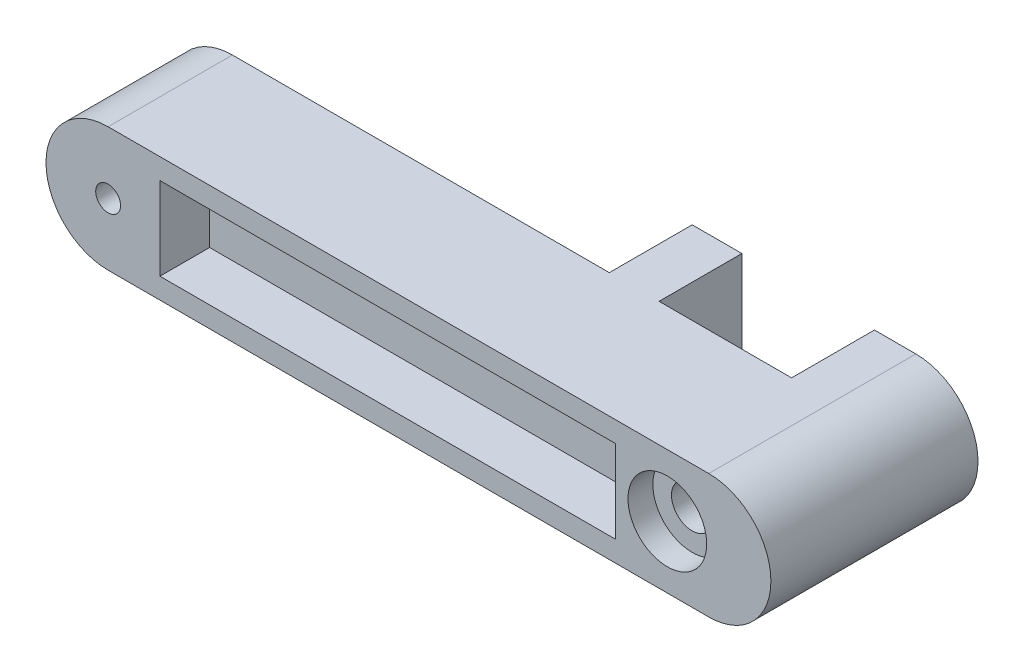
SolidWorks part; units mm, degrees
material "Custom Plastic"
ref_plane "Front Plane" through (0, 0, 0) normal (0, 0, 1) x (1, 0, 0)
ref_plane "Top Plane" through (0, 0, 0) normal (0, 1, 0) x (1, 0, 0)
ref_plane "Right Plane" through (0, 0, 0) normal (1, 0, 0) x (0, 0, -1)
other "Center of Mass"
sketch "Sketch1" plane through (0, 0, 0) normal (1, 0, 0) x (0, 0, -1)
  line L0 (0, 30) -> (135, 30)
  line L1 (135, 0) -> (0, 0)
  arc A0 (135, 30) -> (135, 0) centre (135, 15) cw
  arc A1 (0, 0) -> (0, 30) centre (0, 15) cw
  dimension "D1" = 135
  dimension "D2" = 30
extrude "Boss-Extrude1" add sketch "Sketch1" along normal blind 30
sketch "Sketch2" plane through (30, 0, 0) normal (1, 0, 0) x (0, 0, -1)
  circle A0 centre (0, 15) radius 3
  dimension "D1" = 6
extrude "Cut-Extrude1" cut sketch "Sketch2" against normal blind 30
sketch "Sketch3" plane through (30, 0, 0) normal (1, 0, 0) x (0, 0, -1)
  circle A0 centre (135, 15) radius 9.5
  dimension "D1" = 19
extrude "Cut-Extrude2" cut sketch "Sketch3" against normal blind 6
sketch "Sketch4" plane through (0, 0, 0) normal (-1, 0, 0) x (0, 0, 1)
  circle A0 centre (-135, 15) radius 9.5
  dimension "D1" = 19
extrude "Cut-Extrude3" cut sketch "Sketch4" against normal blind 6
sketch "Sketch5" plane through (6, 0, 0) normal (-1, 0, 0) x (0, 0, 1)
  circle A0 centre (-135, 15) radius 5
  dimension "D1" = 10
extrude "Cut-Extrude4" cut sketch "Sketch5" against normal up to next
scale "Scale1" [suppressed]
sketch "Sketch6" plane through (30, 0, 0) normal (1, 0, 0) x (0, 0, -1)
  line L1 (12.5, 25) -> (122.5, 25)
  line L2 (12.5, 25) -> (12.5, 5)
  line L3 (12.5, 5) -> (122.5, 5)
  line L4 (122.5, 25) -> (122.5, 5)
  line L5 (12.5, 25) -> (122.5, 5) construction
  line L6 (12.5, 5) -> (122.5, 25) construction
  point P0 (67.5, 15)
  dimension "D1" = 20
  dimension "D2" = 110
extrude "Cut-Extrude5" cut sketch "Sketch6" against normal blind 12
sketch "Sketch7" plane through (0, 0, 0) normal (-1, 0, 0) x (0, 0, 1)
  line L1 (-12.5, 5) -> (-122.5, 5)
  line L2 (-12.5, 5) -> (-12.5, 25)
  line L3 (-12.5, 25) -> (-122.5, 25)
  line L4 (-122.5, 5) -> (-122.5, 25)
  line L5 (-12.5, 5) -> (-122.5, 25) construction
  line L6 (-12.5, 25) -> (-122.5, 5) construction
  point P0 (-67.5, 15)
  dimension "D1" = 20
  dimension "D2" = 110
extrude "Cut-Extrude6" cut sketch "Sketch7" against normal blind 12
sketch "Sketch8" plane through (12, 0, 0) normal (-1, 0, 0) x (0, 0, 1)
  line L0 (-135, 30) -> (0, 30) construction
  line L1 (-103, 30) -> (-91, 30)
  line L2 (-103, 30) -> (-103, 0)
  line L3 (-103, 0) -> (-91, 0)
  line L4 (-91, 30) -> (-91, 0)
  line L5 (0, 0) -> (-135, 0) construction
  line L6 (-135, 15) -> (-135, 51.1309) construction
  line L7 (-145, 0) -> (-157, 0)
  line L8 (-145, 0) -> (-145, 30)
  line L9 (-145, 30) -> (-157, 30)
  line L10 (-157, 0) -> (-157, 30)
  line L11 (-91, 30) -> (-175.1648, 30) construction
  line L12 (-91, 0) -> (-167.1663, 0) construction
  dimension "D1" = 32
  dimension "D2" = 10
  dimension "D3" = 12
  dimension "D4" = 12
extrude "Boss-Extrude2" add sketch "Sketch8" along normal blind 32
sketch "Sketch9" plane through (12, 0, 0) normal (1, 0, 0) x (0, 0, -1)
  line L5 (145, 30) -> (145, 26.1803)
  line L6 (145, 3.8197) -> (145, 0)
  line L7 (145, 0) -> (157, 0)
  line L8 (157, 0) -> (157, 30)
  line L9 (157, 30) -> (145, 30)
  line L10 (145, 30) -> (145, 26.1803)
  line L11 (145, 3.8197) -> (145, 0)
  line L12 (145, 0) -> (157, 0)
  line L13 (157, 0) -> (157, 30)
  line L14 (157, 30) -> (145, 30)
  arc A1 (145, 3.8197) -> (145, 26.1803) centre (135, 15) ccw
  arc A2 (145, 3.8197) -> (145, 26.1803) centre (135, 15) ccw
  dimension "D1" = 0
extrude "Cut-Extrude7" cut sketch "Sketch9" against normal blind 35
sketch "Sketch10" plane through (30, 0, 0) normal (1, 0, 0) x (0, 0, -1)
  line L0 (135, 30) -> (145, 30)
  line L1 (145, 0) -> (135, 0)
  arc A0 (135, 0) -> (135, 30) centre (135, 15) ccw construction
  arc A1 (145, 30) -> (145, 0) centre (145, 15) cw
  arc A2 (135, 0) -> (135, 30) centre (135, 15) ccw
  dimension "D1" = 10
extrude "Boss-Extrude3" add sketch "Sketch10" against normal up to surface (50 mm away) up to face at (-20, 15, -147.5)
sketch "Sketch11" plane through (-20, 0, 0) normal (-1, 0, 0) x (0, 0, 1)
  circle A0 centre (-149.85, 10.3502) radius 1.5
  dimension "D1" = 3
sketch "Sketch12" plane through (-20, 0, 0) normal (-1, 0, 0) x (0, 0, 1)
  circle A0 centre (-99.35, 10.3502) radius 1.5
  dimension "D1" = 3
sketch "Sketch13" plane through (-20, 0, 0) normal (-1, 0, 0) x (0, 0, 1)
  circle A0 centre (-149.85, 20.3502) radius 1.5
  circle A1 centre (-99.35, 20.3502) radius 1.5
  dimension "D1" = 3
  dimension "D2" = 3
extrude "Cut-Extrude8" cut sketch "Sketch11" against normal blind 10
extrude "Cut-Extrude9" cut sketch "Sketch13" against normal blind 10
extrude "Cut-Extrude10" cut sketch "Sketch12" against normal blind 10
move or copy body "Body-Move/Copy1" bodies to move or copy 114 copy no rotation origin (5, 0, -72.5) rotation axis (0, -1, 0) rotation angle 90
sketch "Sketch14" plane through (0, 0, -47.5) normal (0, 0, 1) x (1, 0, 0)
  point P0 (-67.5, 15)
move or copy body "Body-Move/Copy2" bodies to move or copy 115 copy no translate (67.5, -15, 47.5)
